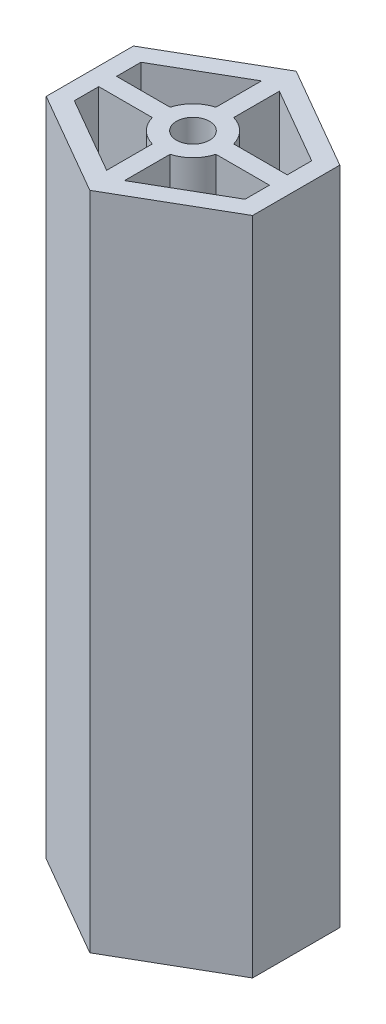
SolidWorks part; units mm, degrees
ref_plane "Front Plane" through (0, 0, 0) normal (0, 0, 1) x (1, 0, 0)
ref_plane "Top Plane" through (0, 0, 0) normal (0, 1, 0) x (1, 0, 0)
ref_plane "Right Plane" through (0, 0, 0) normal (1, 0, 0) x (0, 0, -1)
sketch "Sketch1" plane through (0, 0, 0) normal (0, 1, 0) x (1, 0, 0)
  line L0 (-12.5, 5.2831) -> (-12.5, -5.2831)
  line L1 (-12.5, 12.5) -> (12.5, 12.5) construction
  line L2 (-12.5, 12.5) -> (-12.5, -12.5) construction
  line L3 (-12.5, -12.5) -> (12.5, -12.5) construction
  line L4 (12.5, 12.5) -> (12.5, -12.5) construction
  line L5 (-12.5, -5.2831) -> (0, -12.5)
  line L6 (-12.5, 5.2831) -> (0, 12.5)
  line L7 (0, 4.0578) -> (0, -4.1758) construction
  line L8 (12.5, -5.2831) -> (0, -12.5)
  line L9 (12.5, 5.2831) -> (12.5, -5.2831)
  line L10 (12.5, 5.2831) -> (0, 12.5)
  line L11 (-1.08, 9.3823) -> (-1.08, 3.8514)
  line L12 (1.08, 9.3823) -> (1.08, 3.8514)
  line L13 (-10.34, 1.08) -> (-3.8514, 1.08)
  line L14 (-10.34, -1.08) -> (-3.8514, -1.08)
  line L15 (-1.08, -3.8514) -> (-1.08, -9.3823)
  line L16 (1.08, -3.8514) -> (1.08, -9.3823)
  line L17 (3.8514, 1.08) -> (10.34, 1.08)
  line L18 (3.8514, -1.08) -> (10.34, -1.08)
  line L19 (-10.34, 4.036) -> (-1.08, 9.3823)
  line L20 (10.34, 4.036) -> (1.08, 9.3823)
  line L21 (10.34, 4.036) -> (10.34, 1.08)
  line L22 (10.34, -4.036) -> (1.08, -9.3823)
  line L23 (-10.34, -4.036) -> (-1.08, -9.3823)
  line L24 (-10.34, 4.036) -> (-10.34, 1.08)
  line L25 (-10.34, -1.08) -> (-10.34, -4.036)
  line L26 (-10.34, 4.036) -> (-10.34, -4.036) construction
  line L27 (-10.34, -4.036) -> (0, -10.0058) construction
  line L28 (10.34, -4.036) -> (0, -10.0058) construction
  line L29 (10.34, -1.08) -> (10.34, -4.036)
  line L30 (10.34, 4.036) -> (10.34, -4.036) construction
  line L31 (-10.34, 4.036) -> (0, 10.0058) construction
  line L32 (10.34, 4.036) -> (0, 10.0058) construction
  arc A0 (-3.8514, -1.08) -> (-1.08, -3.8514) centre (0, 0) ccw
  circle A1 centre (0, 0) radius 2
  arc A2 (-1.08, 3.8514) -> (-3.8514, 1.08) centre (0, 0) ccw
  arc A3 (3.8514, 1.08) -> (1.08, 3.8514) centre (0, 0) ccw
  arc A4 (1.08, -3.8514) -> (3.8514, -1.08) centre (0, 0) ccw
  point P4 (-12.5, 0)
  point P5 (0, -12.5)
  point P13 (0, 12.5)
  dimension "D4" = 8
  dimension "D9" = 4
  dimension "D1" = 25
  dimension "D2" = 120
  dimension "D3" = 120
  dimension "D5" = 2.16
  dimension "D6" = 1.08
  dimension "D7" = 2.16
  dimension "D8" = 1.08
  dimension "D10" = 2.16
extrude "Boss-Extrude2" add sketch "Sketch1" along normal blind 80
equation "\"diameter\" = 3mm"
equation "\"D9@Sketch1\"=\"diameter\"+1mm"
equation "\"D4@Sketch1\"=(\"diameter\"+1mm)*2"
